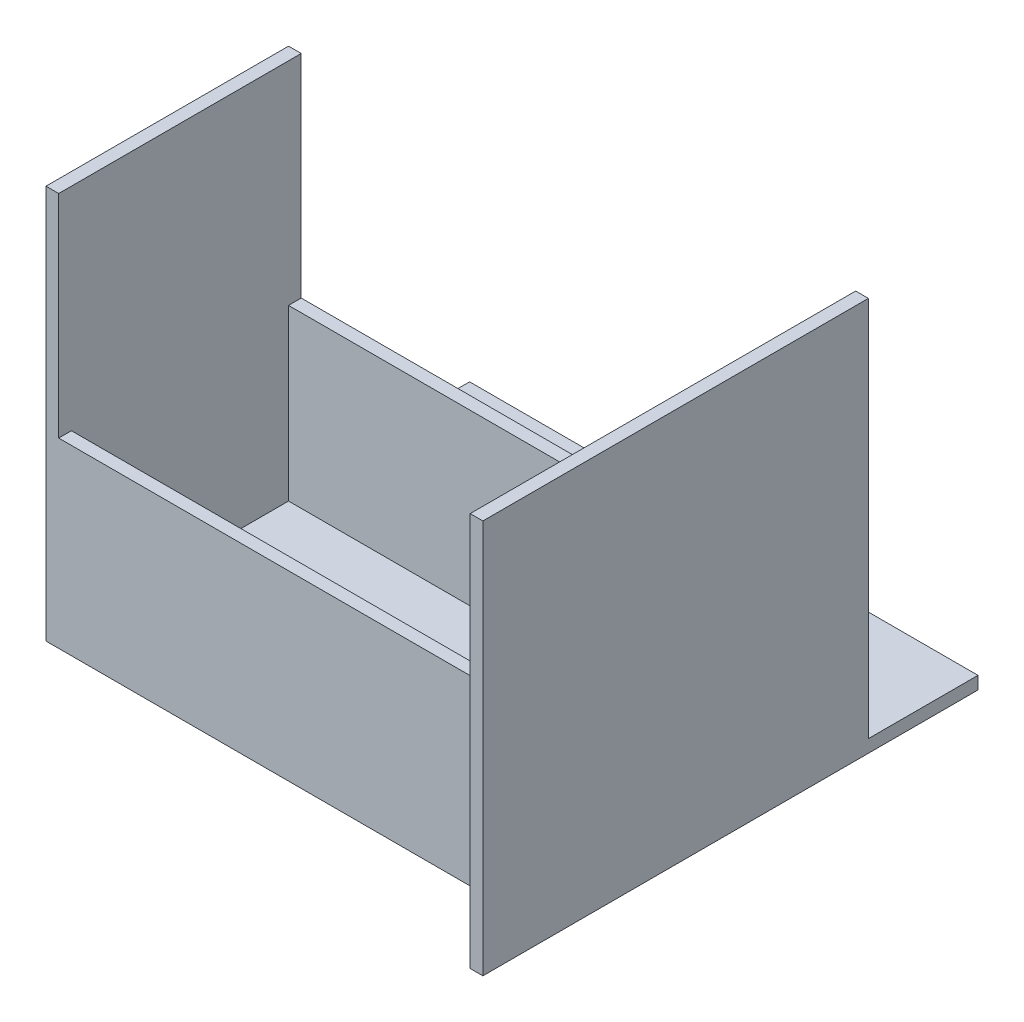
SolidWorks part; units mm, degrees
ref_plane "Front Plane" through (0, 0, 0) normal (0, 0, 1) x (1, 0, 0)
ref_plane "Top Plane" through (0, 0, 0) normal (0, 1, 0) x (1, 0, 0)
ref_plane "Right Plane" through (0, 0, 0) normal (1, 0, 0) x (0, 0, -1)
sketch "Sketch1" plane through (0, 0, 0) normal (0, 1, 0) x (1, 0, 0)
  line L1 (0, 0) -> (120, 0)
  line L2 (0, 0) -> (0, 100)
  line L3 (0, 100) -> (120, 100)
  line L4 (120, 0) -> (120, 100)
  dimension "D1" = 120
  dimension "D2" = 100
extrude "Boss-Extrude1" add sketch "Sketch1" along normal blind 3
sketch "Sketch2" plane through (0, 3, 0) normal (0, 1, 0) x (1, 0, 0)
  line L0 (0, 100) -> (0, 0) construction
  line L1 (0, 57.25) -> (117, 57.25)
  line L2 (0, 57.25) -> (0, 54.25)
  line L5 (120, 0) -> (120, 100) construction
  line L6 (0, 0) -> (120, 0) construction
  line L7 (0, 54.25) -> (3, 54.25)
  line L8 (0, 54.25) -> (0, 0)
  line L9 (0, 0) -> (3, 0)
  line L10 (3, 54.25) -> (3, 0)
  line L11 (117, 57.25) -> (117, 54.25)
  line L12 (3, 3) -> (120, 3)
  line L13 (3, 3) -> (3, 0)
  line L14 (3, 0) -> (120, 0)
  line L15 (120, 3) -> (120, 0)
  line L16 (117, 57.25) -> (120, 57.25)
  line L17 (117, 57.25) -> (117, 3)
  line L18 (117, 3) -> (120, 3)
  line L19 (120, 57.25) -> (120, 3)
  line L20 (117, 54.25) -> (0, 54.25)
  point P16 (111.4179, 64.6266)
  point P17 (110.1746, 76.59)
  line M19 (0, 100) -> (0, 0)
  line M20 (0, 0) -> (120, 0)
  line M21 (120, 0) -> (120, 100)
  dimension "D1" = 51.25
  dimension "D2" = 3
extrude "Boss-Extrude2" add sketch "Sketch2" along normal blind 40 contours L20 L11 L1 L7 M19 | L10 L7 M19 M20 | L12 L10 M20 M21 | L11 L17 L12 L16 M21
sketch "Sketch3" plane through (0, 43, 0) normal (0, 1, 0) x (1, 0, 0)
  line L0 (0, 0) -> (120, 0) construction
  line L1 (0, 57.25) -> (3, 57.25)
  line L2 (0, 57.25) -> (0, 0)
  line L3 (0, 0) -> (3, 0)
  line L4 (3, 57.25) -> (3, 0)
  line L5 (3, 54.25) -> (3, 3) construction
extrude "Boss-Extrude3" add sketch "Sketch3" along normal blind 50
sketch "Sketch4" plane through (0, 0, 0) normal (0, -1, 0) x (1, 0, 0)
  line L1 (120, 0) -> (120, -100) construction
  line L2 (120, 16.875) -> (117, 16.875)
  line L3 (120, 16.875) -> (120, -74.125)
  line L4 (120, -74.125) -> (117, -74.125)
  line L5 (117, 16.875) -> (117, -74.125)
  line L6 (117, -54.25) -> (117, -3) construction
  line L7 (117, -54.25) -> (117, -3)
  point P5 (118.5311, 29.398)
  point P10 (117, -28.625)
  point P11 (117, -28.625)
  point P12 (120, 7.1833)
  line M7 (120, -100) -> (120, 0)
  line M8 (120, 0) -> (0, 0)
  dimension "D1" = 3
  dimension "D2" = 91
extrude "Boss-Extrude4" add sketch "Sketch4" against normal up to surface (93 mm away) contours L2 L5 L3 M8 | L5 L4 M8 M7 up to face at (1.5, 93, -28.625)
